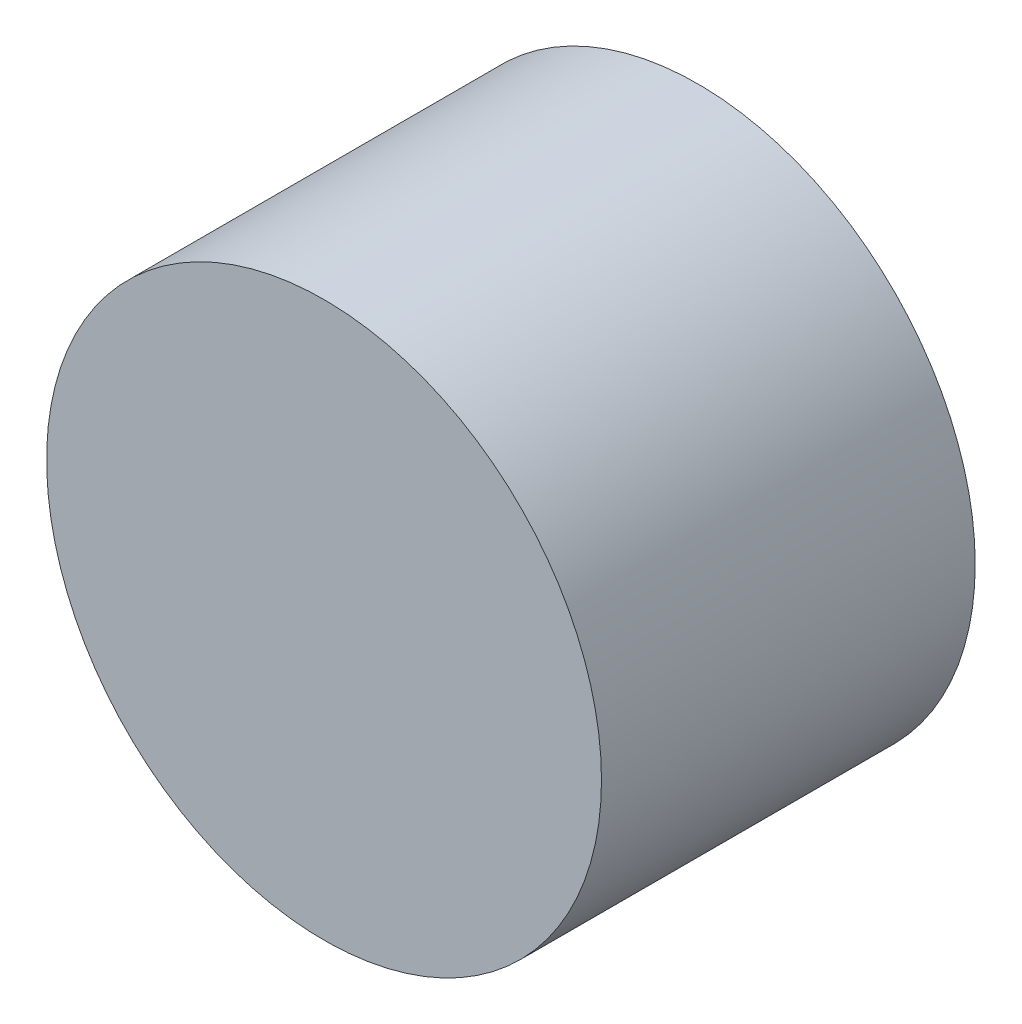
SolidWorks part; units mm, degrees
ref_plane "Front Plane" through (0, 0, 0) normal (0, 0, 1) x (1, 0, 0)
ref_plane "Top Plane" through (0, 0, 0) normal (0, 1, 0) x (1, 0, 0)
ref_plane "Right Plane" through (0, 0, 0) normal (1, 0, 0) x (0, 0, -1)
sketch "Sketch1" plane through (0, 0, 0) normal (0, 0, 1) x (1, 0, 0)
  circle A0 centre (0, 0) radius 11.1359
extrude "Boss-Extrude1" add sketch "Sketch1" against normal blind 15
